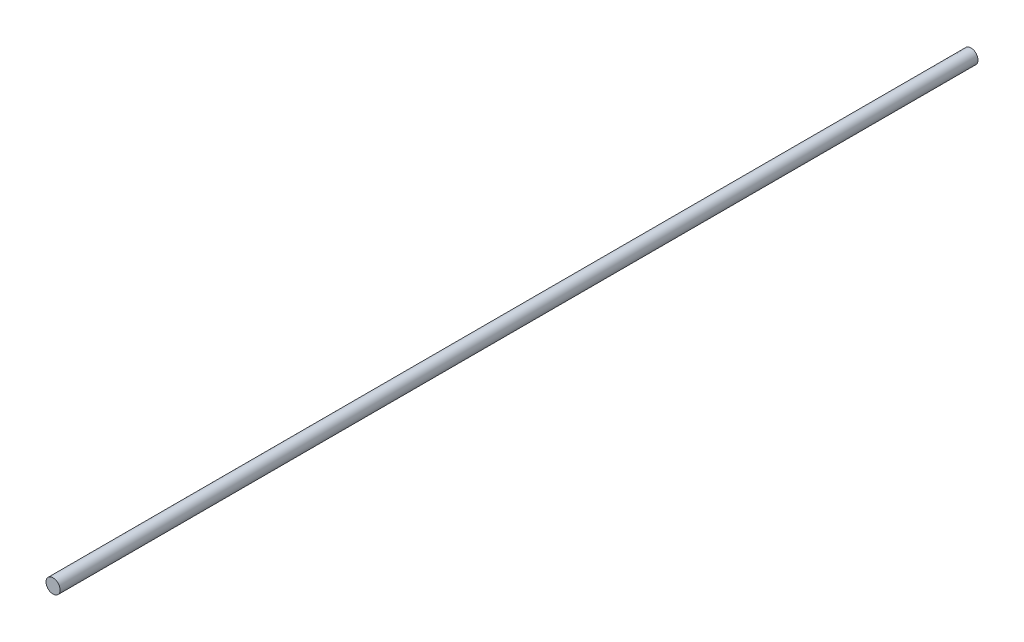
SolidWorks part; units mm, degrees
material "Plain Carbon Steel"
ref_plane "Front Plane" through (0, 0, 0) normal (0, 0, 1) x (1, 0, 0)
ref_plane "Top Plane" through (0, 0, 0) normal (0, 1, 0) x (1, 0, 0)
ref_plane "Right Plane" through (0, 0, 0) normal (1, 0, 0) x (0, 0, -1)
sketch "Sketch1" plane through (0, 0, 0) normal (0, 0, 1) x (1, 0, 0)
  circle A0 centre (0, 0) radius 4
  dimension "D1" = 8
extrude "Boss-Extrude1" add sketch "Sketch1" along normal blind 520
